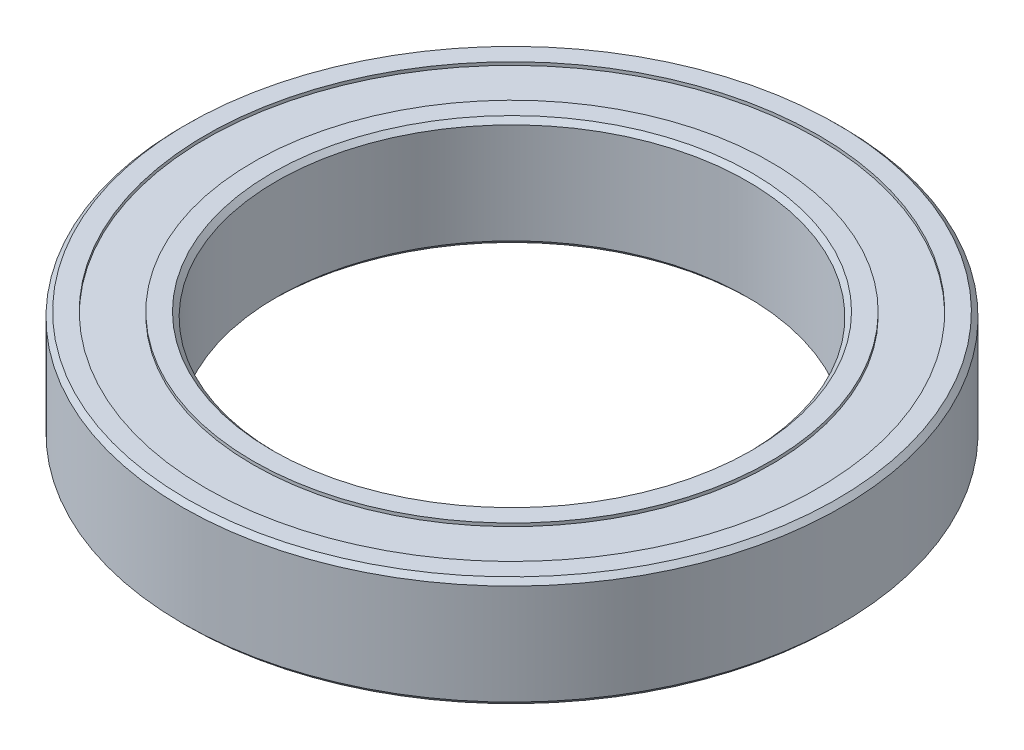
SolidWorks part; units mm, degrees
ref_plane "Front Plane" through (0, 0, 0) normal (0, 0, 1) x (1, 0, 0)
ref_plane "Top Plane" through (0, 0, 0) normal (0, 1, 0) x (1, 0, 0)
ref_plane "Right Plane" through (0, 0, 0) normal (1, 0, 0) x (0, 0, -1)
sketch "Sketch1" plane through (0, 0, 0) normal (0, 1, 0) x (1, 0, 0)
  circle A0 centre (0, 0) radius 15
  circle A1 centre (0, 0) radius 21
  dimension "D1" = 42
  dimension "D2" = 30
extrude "Boss-Extrude1" add sketch "Sketch1" along normal blind 7
sketch "Sketch2" plane through (0, 7, 0) normal (0, 1, 0) x (1, 0, 0)
  circle A2 centre (0, 0) radius 16.5
  circle A3 centre (0, 0) radius 16.5
  circle A5 centre (0, 0) radius 19.5
  circle A6 centre (0, 0) radius 19.5
  dimension "D1" = 1.5
  dimension "D2" = 1.5
extrude "Cut-Extrude1" cut sketch "Sketch2" against normal blind 0.2
chamfer "Chamfer1" distance 0.3 angle 45
sketch "Sketch3" plane through (0, 0, 0) normal (0, -1, 0) x (1, 0, 0)
  circle A0 centre (0, 0) radius 16.5 construction
  circle A1 centre (0, 0) radius 19.5
  circle A2 centre (0, 0) radius 19.5
  circle A3 centre (0, 0) radius 16.5
  dimension "D1" = 0
extrude "Cut-Extrude2" cut sketch "Sketch3" against normal blind 0.2
